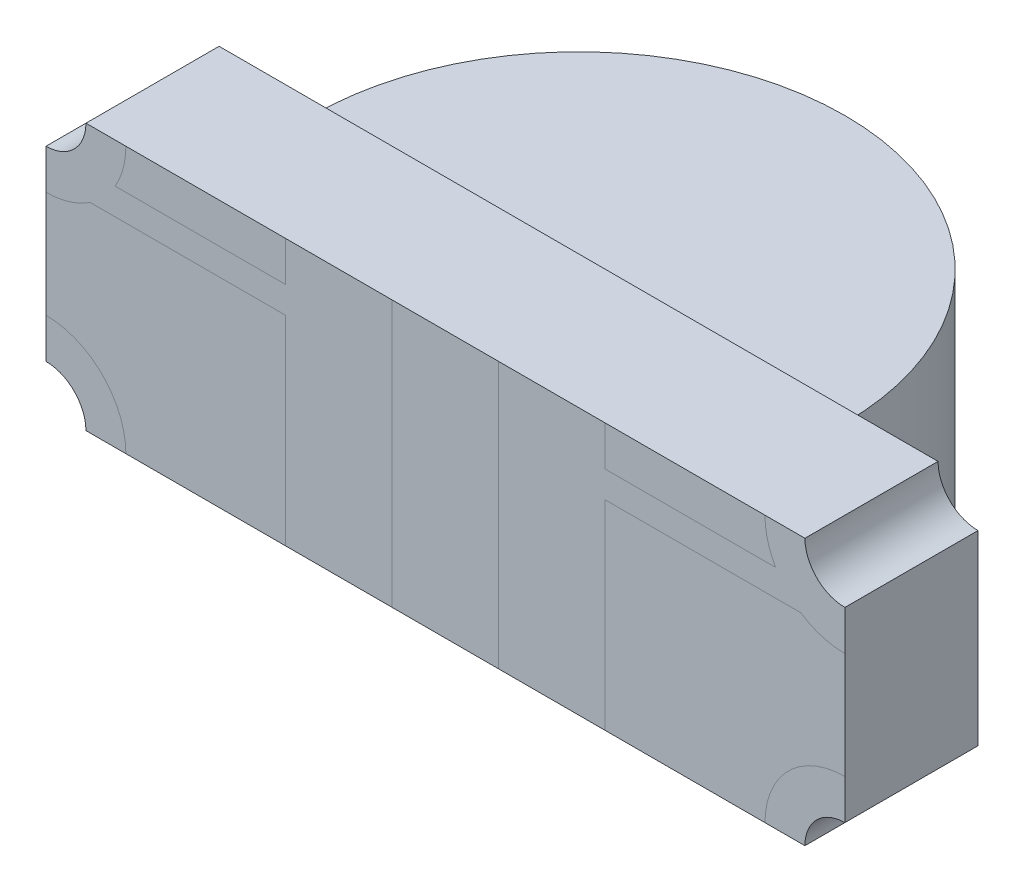
SolidWorks part; units mm, degrees
ref_plane "Front Plane" through (0, 0, 0) normal (0, 0, 1) x (1, 0, 0)
ref_plane "Top Plane" through (0, 0, 0) normal (0, 1, 0) x (1, 0, 0)
ref_plane "Right Plane" through (0, 0, 0) normal (1, 0, 0) x (0, 0, -1)
sketch "Sketch1" plane through (0, 0, 0) normal (0, 1, 0) x (1, 0, 0)
  line L0 (1, 0.5) -> (1.5, 0.5)
  line L1 (-1.5, 0.5) -> (-1, 0.5)
  line L2 (-1.5, 0.5) -> (-1.5, 0)
  line L3 (-1.5, 0) -> (1.5, 0)
  line L4 (1.5, 0.5) -> (1.5, 0)
  line L5 (1, 0.5) -> (-1, 0.5) construction
  line L6 (0, 0.5) -> (0, 0) construction
  arc A0 (1, 0.5) -> (-1, 0.5) centre (0, 0.5) ccw
  point P8 (0, 1.5)
  dimension "D1" = 0.5
  dimension "D2" = 3
  dimension "D3" = 1.5
extrude "Boss-Extrude1" add sketch "Sketch1" along normal blind 1
sketch "Sketch2" plane through (0, 0, 0) normal (0, 0, 1) x (1, 0, 0)
  circle A0 centre (1.5, 1) radius 0.15
  circle A1 centre (1.5, 0) radius 0.15
  circle A2 centre (-1.5, 1) radius 0.15
  circle A3 centre (-1.5, 0) radius 0.15
  dimension "D1" = 0.3
extrude "Cut-Extrude1" cut sketch "Sketch2" against normal through all
sketch "Sketch3" plane through (0, 0, 0) normal (0, 0, 1) x (1, 0, 0)
  line L0 (-1.2402, 0.85) -> (-0.6, 0.85)
  line L1 (-0.6, 0.85) -> (-0.6, 1)
  line L2 (-1.35, 1) -> (1.35, 1) construction
  line L3 (-0.6, 1) -> (-0.2, 1)
  line L4 (-0.2, 1) -> (-0.2, 0)
  line L5 (-1.35, 0) -> (1.35, 0) construction
  line L6 (-0.2, 0) -> (-0.6, 0)
  line L7 (-0.6, 0) -> (-0.6, 0.75)
  line L8 (-0.6, 0.75) -> (-1.3342, 0.75)
  line L9 (1.3342, 0.75) -> (0.6, 0.75)
  line L10 (0.6, 0.75) -> (0.6, 0)
  line L11 (0.6, 0) -> (0.2, 0)
  line L12 (0.2, 0) -> (0.2, 1)
  line L13 (0.2, 1) -> (0.6, 1)
  line L14 (0.6, 1) -> (0.6, 0.85)
  line L15 (0.6, 0.85) -> (1.2402, 0.85)
  arc A0 (1.3342, 0.75) -> (1.2402, 0.85) centre (1.5, 1) ccw
  circle A1 centre (1.5, 0) radius 0.3
  circle A2 centre (-1.5, 0) radius 0.3
  arc A3 (-1.2402, 0.85) -> (-1.3342, 0.75) centre (-1.5, 1) ccw
  dimension "D1" = 0.6
  dimension "D2" = 0.4
  dimension "D3" = 0.4
  dimension "D4" = 0.75
  dimension "D5" = 0.1
split line "Split Line1"
sketch "Sketch4" plane through (0, 1, 0) normal (0, 1, 0) x (1, 0, 0)
  line L0 (1, 0.5) -> (-1, 0.5)
  arc A0 (1, 0.5) -> (-1, 0.5) centre (0, 0.5) ccw
extrude "Cut-Extrude2" cut sketch "Sketch4" against normal blind 0.05
